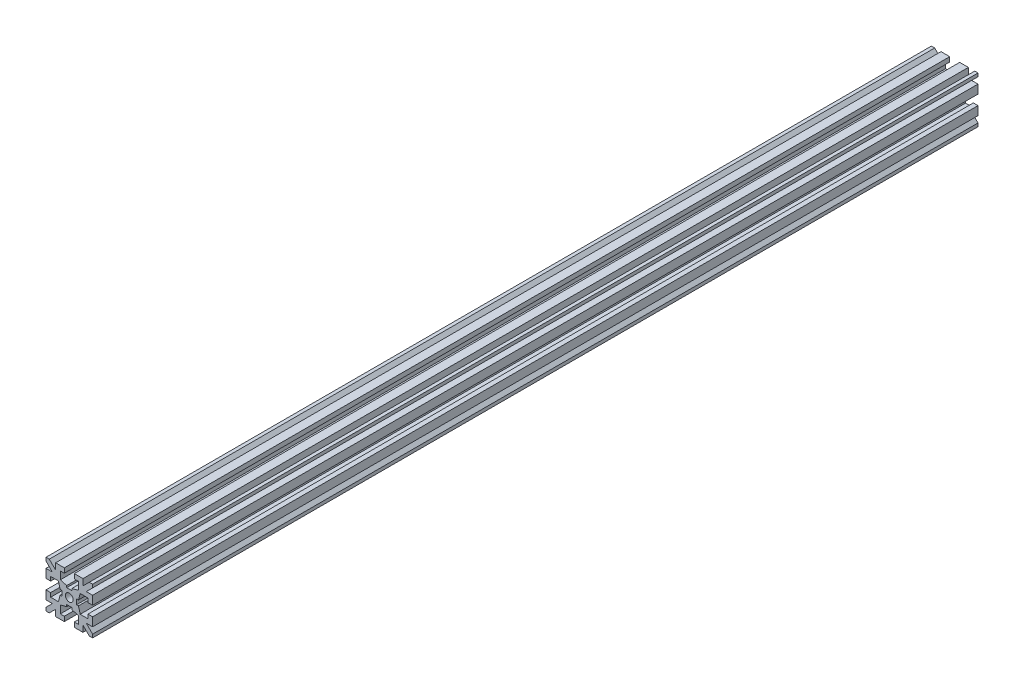
SolidWorks part; units mm, degrees
material "3.0205 (EN-AW 1200)"
ref_plane "Plano frontal" through (0, 0, 0) normal (0, 0, 1) x (1, 0, 0)
ref_plane "Plano superior" through (0, 0, 0) normal (0, 1, 0) x (1, 0, 0)
ref_plane "Plano direito" through (0, 0, 0) normal (1, 0, 0) x (0, 0, -1)
sketch "Esboço1" plane through (0, 0, 0) normal (0, 0, 1) x (1, 0, 0)
  line L0 (-25.7554, 0) -> (0, 0) construction
  line L1 (0, 0) -> (0, 21.5914) construction
  line L2 (0, 2.35) -> (-0.825, 2.35)
  line L3 (-0.825, 2.35) -> (-0.825, 2.95)
  line L4 (-0.825, 2.95) -> (-2.9, 3.5)
  line L5 (-2.9, 3.5) -> (-2.9, 6)
  line L6 (-2.9, 6) -> (-1.6, 6)
  line L7 (-1.6, 6) -> (-1.6, 7.5)
  line L8 (-1.6, 7.5) -> (-4.4, 7.5)
  line L9 (-4.4, 7.5) -> (-4.4, 5.4607)
  line L10 (-4.4, 5.4607) -> (-6.4393, 7.5)
  line L11 (-6.4393, 7.5) -> (-7.5, 7.5)
  line L12 (-7.5, 7.5) -> (0, 0) construction
  line L13 (-2.35, 0) -> (-2.35, 0.825)
  line L14 (-7.5, 6.4393) -> (-7.5, 7.5)
  line L15 (-5.4607, 4.4) -> (-7.5, 6.4393)
  line L16 (-7.5, 4.4) -> (-5.4607, 4.4)
  line L17 (-7.5, 1.6) -> (-7.5, 4.4)
  line L18 (-6, 1.6) -> (-7.5, 1.6)
  line L19 (-6, 2.9) -> (-6, 1.6)
  line L20 (-3.5, 2.9) -> (-6, 2.9)
  line L21 (-2.95, 0.825) -> (-3.5, 2.9)
  line L22 (-2.35, 0.825) -> (-2.95, 0.825)
  line L23 (-2.35, 0) -> (0, 0)
  line L24 (0, 0) -> (0, 2.35)
  dimension "D1" = 45
  dimension "D2" = 4.7
  dimension "D3" = 5.8
  dimension "D4" = 15
  dimension "D5" = 3.1
  dimension "D6" = 3.2
  dimension "D7" = 0.6
  dimension "D8" = 1.65
  dimension "D9" = 1.5
  dimension "D10" = 2.5
  dimension "D11" = 1.5
extrude "Ressalto-extrusão1" add sketch "Esboço1" along normal mid plane 285
mirror "Espelhar1" about plane through (0, 0, 0) normal (0, 1, 0) of "Ressalto-extrusão1"
mirror "Espelhar2" about plane through (0, 0, 0) normal (1, 0, 0) of "Espelhar1", "Ressalto-extrusão1"
sketch "Esboço2" plane through (0, 0, 142.5) normal (0, 0, 1) x (1, 0, 0)
  circle A0 centre (0, 0) radius 1.25
  dimension "D1" = 2.5
extrude "Corte-extrusão1" cut sketch "Esboço2" against normal through all both and the other way through all
